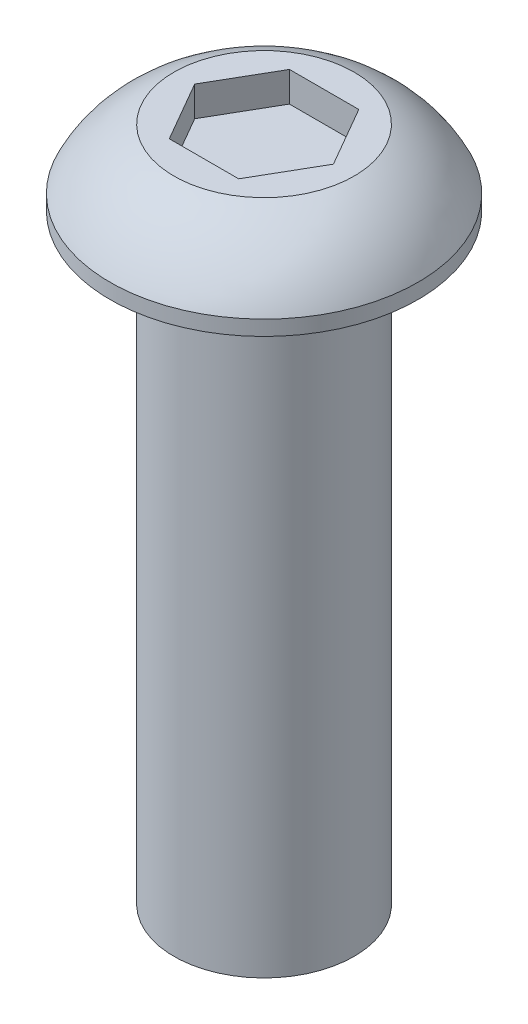
SolidWorks part; units mm, degrees
material "AISI 304"
ref_plane "Front Plane" through (0, 0, 0) normal (0, 0, 1) x (1, 0, 0)
ref_plane "Top Plane" through (0, 0, 0) normal (0, 1, 0) x (1, 0, 0)
ref_plane "Right Plane" through (0, 0, 0) normal (1, 0, 0) x (0, 0, -1)
sketch "Sketch1" plane through (0, 0, 0) normal (0, 0, 1) x (1, 0, 0)
  line L0 (3, 0) -> (5.125, 0)
  line L1 (5.125, 0) -> (5.125, 0.5)
  line L2 (3, 2.5) -> (0, 2.5)
  line L3 (3, 0) -> (3, -20)
  line L4 (3, -20) -> (0, -20)
  line L5 (0, -20) -> (0, 2.5)
  arc A0 (5.125, 0.5) -> (3, 2.5) centre (1.5099, -1.2121) ccw
  point P9 (2, 0.5)
  point P10 (1.4054, -0.7047)
  point P11 (3.8, 1.3476)
  point P12 (3.8, 0.6755)
  point P13 (1.1081, 2.5)
  point P14 (1.5217, 2.5)
  point P15 (3.8, 0.6625)
  dimension "D5" = 4
  dimension "D1" = 3
  dimension "D2" = 20
  dimension "D3" = 5.125
  dimension "D4" = 2.5
  dimension "D6" = 3
  dimension "D7" = 0.5
revolve "Revolve1" add sketch "Sketch1" angle 360 about L5
sketch "Sketch2" plane through (0, 2.5, 0) normal (0, 1, 0) x (1, 0, 0)
  line L1 (1.1547, 2) -> (-1.1547, 2)
  line L2 (-1.1547, 2) -> (-2.3094, 0)
  line L3 (-2.3094, 0) -> (-1.1547, -2)
  line L4 (-1.1547, -2) -> (1.1547, -2)
  line L5 (1.1547, -2) -> (2.3094, 0)
  line L6 (2.3094, 0) -> (1.1547, 2)
  circle A0 centre (0, 0) radius 2 construction
  dimension "D1" = 4
extrude "Cut-Extrude1" cut sketch "Sketch2" against normal blind 1
